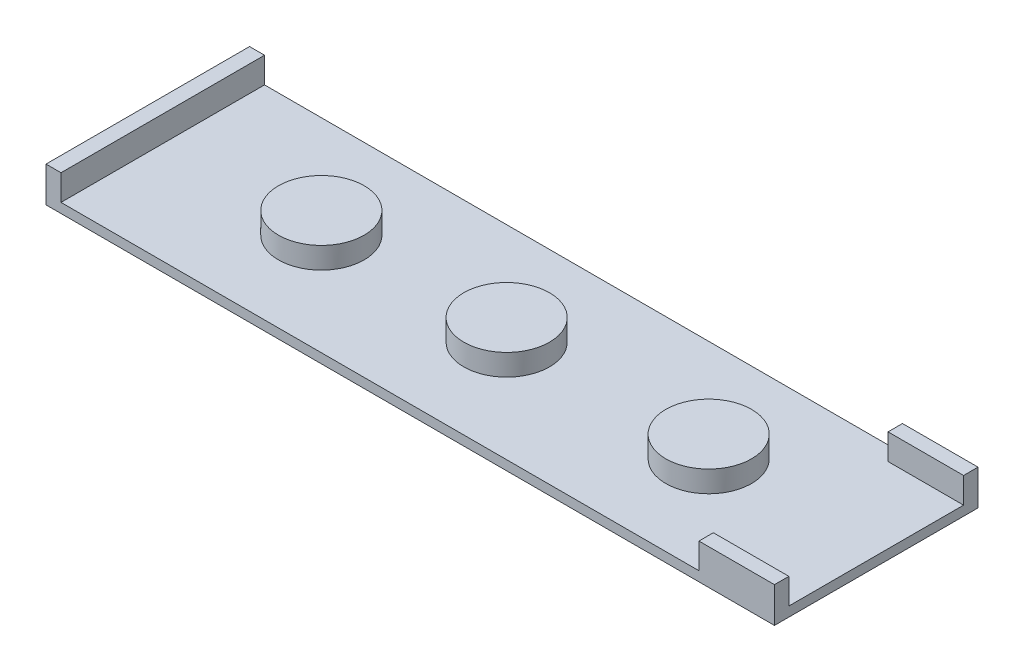
SolidWorks part; units mm, degrees
ref_plane "Front Plane" through (0, 0, 0) normal (0, 0, 1) x (1, 0, 0)
ref_plane "Top Plane" through (0, 0, 0) normal (0, 1, 0) x (1, 0, 0)
ref_plane "Right Plane" through (0, 0, 0) normal (1, 0, 0) x (0, 0, -1)
sketch "Sketch1" plane through (0, 0, 0) normal (0, 1, 0) x (1, 0, 0)
  line L1 (-11.857, -5.7662) -> (22.143, -5.7662)
  line L2 (-11.857, -5.7662) -> (-11.857, 3.7338)
  line L3 (-11.857, 3.7338) -> (22.143, 3.7338)
  line L4 (22.143, -5.7662) -> (22.143, 3.7338)
  dimension "D1" = 9.5
  dimension "D2" = 34
extrude "Boss-Extrude1" add sketch "Sketch1" along normal blind 0.45
sketch "Sketch2" plane through (0, 0.45, 0) normal (0, 1, 0) x (1, 0, 0)
  line L0 (-11.857, -5.7662) -> (22.143, -5.7662) construction
  line L1 (-11.857, 3.7338) -> (-11.157, 3.7338)
  line L2 (-11.857, 3.7338) -> (-11.857, -5.7662)
  line L3 (-11.857, -5.7662) -> (-11.157, -5.7662)
  line L4 (-11.157, 3.7338) -> (-11.157, -5.7662)
  dimension "D1" = 0.7
extrude "Boss-Extrude2" add sketch "Sketch2" along normal blind 1.2
sketch "Sketch3" plane through (0, 0.45, 0) normal (0, 1, 0) x (1, 0, 0)
  line L0 (-11.157, -5.7662) -> (22.143, -5.7662) construction
  line L1 (-11.857, 3.7338) -> (-11.857, -5.7662) construction
  circle A0 centre (-3.757, -1.0162) radius 2
  circle A1 centre (4.893, -1.0162) radius 2
  circle A2 centre (14.323, -1.0162) radius 2
  dimension "D1" = 4.75
  dimension "D2" = 8.1
  dimension "D3" = 16.75
  dimension "D4" = 26.18
  dimension "D5" = 4
  dimension "D6" = 4
  dimension "D7" = 4
extrude "Boss-Extrude3" add sketch "Sketch3" along normal blind 1
sketch "Sketch4" plane through (0, 0.45, 0) normal (0, 1, 0) x (1, 0, 0)
  line L1 (22.143, 3.7338) -> (18.6182, 3.7338)
  line L2 (22.143, 3.7338) -> (22.143, 3.0604)
  line L3 (22.143, 3.0604) -> (18.6182, 3.0604)
  line L4 (18.6182, 3.7338) -> (18.6182, 3.0604)
  line L5 (22.143, -5.7662) -> (18.6182, -5.7662)
  line L6 (22.143, -5.7662) -> (22.143, -5.094)
  line L7 (22.143, -5.094) -> (18.6182, -5.094)
  line L8 (18.6182, -5.7662) -> (18.6182, -5.094)
extrude "Boss-Extrude4" add sketch "Sketch4" along normal blind 1.2
